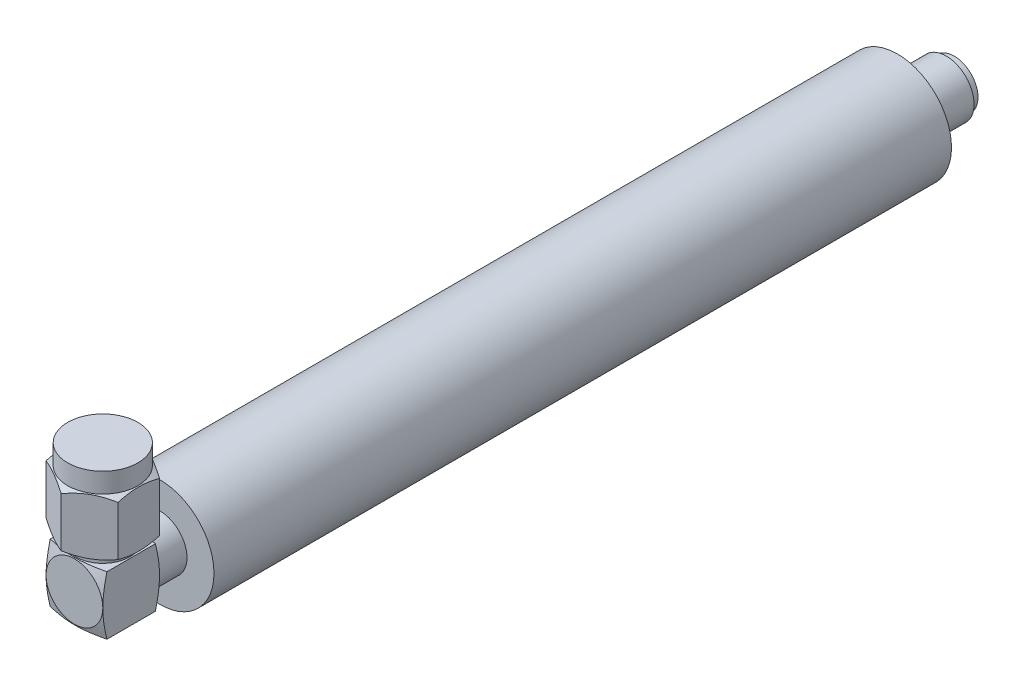
SolidWorks part; units mm, degrees
ref_plane "Front Plane" through (0, 0, 0) normal (0, 0, 1) x (1, 0, 0)
ref_plane "Top Plane" through (0, 0, 0) normal (0, 1, 0) x (1, 0, 0)
ref_plane "Right Plane" through (0, 0, 0) normal (1, 0, 0) x (0, 0, -1)
sketch "Sketch1" plane through (0, 0, 0) normal (0, 0, 1) x (1, 0, 0)
  circle A0 centre (0, 0) radius 6
  dimension "D1" = 12
extrude "Boss-Extrude1" add sketch "Sketch1" along normal blind 81.92
sketch "Sketch2" plane through (0, 0, 0) normal (0, 1, 0) x (1, 0, 0)
  line L0 (0, -88.8627) -> (0, -94.8627) construction
  line L1 (-1.9871, 0) -> (-1.9871, 1.5)
  line L2 (6, 0) -> (-6, 0) construction
  line L3 (-1.9871, 1.5) -> (-3.1, 1.5)
  line L4 (-3.1, 1.5) -> (-3.1, 6.3)
  line L5 (-3.1, 6.3) -> (0, 6.3)
  line L6 (-1.9871, 0) -> (0, 0)
  line L7 (0, 6.3) -> (0, 0)
  dimension "D1" = 6.3
  dimension "D2" = 1.5
  dimension "D3" = 6.2
revolve "Revolve1" add sketch "Sketch2" angle 360 about L0
sketch "Sketch3" plane through (0, 0, 81.92) normal (0, 0, 1) x (1, 0, 0)
  circle A0 centre (0, 0) radius 3
  dimension "D1" = 6
extrude "Boss-Extrude2" add sketch "Sketch3" along normal blind 3.2
sketch "Sketch4" plane through (0, 0, 0) normal (0, 1, 0) x (1, 0, 0)
  line L0 (-3, -85.12) -> (3, -85.12) construction
  line L1 (-3.15, -91.42) -> (3.15, -91.42)
  line L2 (-3.15, -91.42) -> (-3.15, -85.12)
  line L3 (-3.15, -85.12) -> (3.15, -85.12)
  line L4 (3.15, -91.42) -> (3.15, -85.12)
  line L5 (-3.15, -91.42) -> (3.15, -85.12) construction
  line L6 (-3.15, -85.12) -> (3.15, -91.42) construction
  line L7 (-3, -81.92) -> (3, -81.92) construction
  point P0 (0, -88.27)
  dimension "D1" = 6.3
  dimension "D2" = 6.3
  dimension "D3" = 6.35
extrude "Boss-Extrude3" add sketch "Sketch4" along normal mid plane 6.5
sketch "Sketch9" plane through (0, 0, 0) normal (0, 1, 0) x (1, 0, 0)
  line L0 (0, -97.0404) -> (0, -73.5237) construction
  line L1 (-3.15, -91.42) -> (-4.65, -90.92)
  line L4 (-4.65, -90.92) -> (-4.65, -91.42)
  line L5 (-4.65, -91.42) -> (-3.15, -91.42)
  line L6 (-3.15, -85.12) -> (-4.65, -85.12)
  line L8 (-4.65, -85.12) -> (-4.65, -85.62)
  line L9 (-3.15, -85.12) -> (-4.65, -85.62)
  dimension "D1" = 1.5
  dimension "D2" = 0.5
  dimension "D3" = 1.5
  dimension "D4" = 0.5
  dimension "D5" = 3.15
  dimension "D6" = 3.15
revolve "Cut-Revolve3" cut sketch "Sketch9" angle 360 about L0
sketch "Sketch10" plane through (0, 3.25, 0) normal (0, 1, 0) x (1, 0, 0)
  line L0 (-3, -81.92) -> (3, -81.92) construction
  circle A0 centre (0, -88.27) radius 3
  dimension "D1" = 6
  dimension "D2" = 6.35
extrude "Boss-Extrude6" add sketch "Sketch10" along normal mid plane 2
sketch "Sketch11" plane through (0, 4.25, 0) normal (0, 1, 0) x (1, 0, 0)
  line L1 (0, -83.6512) -> (-4, -85.9606)
  line L2 (-4, -85.9606) -> (-4, -90.5794)
  line L3 (-4, -90.5794) -> (0, -92.8888)
  line L4 (0, -92.8888) -> (4, -90.5794)
  line L5 (4, -90.5794) -> (4, -85.9606)
  line L6 (4, -85.9606) -> (0, -83.6512)
  circle A0 centre (0, -88.27) radius 4 construction
  point P1 (2, -84.8059)
  dimension "D1" = 8
extrude "Boss-Extrude7" add sketch "Sketch11" along normal blind 8.5
sketch "Sketch12" plane through (0, 12.75, 0) normal (0, 1, 0) x (1, 0, 0)
  line L0 (-3, -81.92) -> (3, -81.92) construction
  circle A0 centre (0, -88.27) radius 3.9
  circle A1 centre (0, -88.27) radius 5.6457
  dimension "D2" = 7.8
  dimension "D1" = 6.35
extrude "Cut-Extrude2" cut sketch "Sketch12" against normal blind 2.2
sketch "Sketch13" plane through (0, 0, 0) normal (1, 0, 0) x (0, 0, -1)
  line L0 (-92.17, 10.55) -> (-92.8888, 10.15)
  line L1 (-92.8888, 10.55) -> (-92.8888, 4.25) construction
  line L2 (-92.8888, 10.15) -> (-92.8888, 10.55)
  line L3 (-92.8888, 10.55) -> (-92.17, 10.55)
  line L4 (-88.27, 13.7522) -> (-88.27, 2.0185) construction
  line L5 (-92.8888, 4.65) -> (-92.17, 4.25)
  line L6 (-92.8888, 4.25) -> (-90.5794, 4.25) construction
  line L7 (-92.17, 4.25) -> (-92.8888, 4.25)
  line L8 (-92.8888, 4.25) -> (-92.8888, 4.65)
  dimension "D1" = 0.4
  dimension "D2" = 0.4
  dimension "D3" = 3.9
revolve "Cut-Revolve4" cut sketch "Sketch13" angle 360 about L4
sketch "Sketch14" plane through (0, 0, -6.3) normal (0, 0, -1) x (-1, 0, 0)
  circle A0 centre (0, 0) radius 2.65
  circle A1 centre (0, 0) radius 3.9598
  dimension "D1" = 5.3
extrude "Cut-Extrude3" cut sketch "Sketch14" against normal blind 0.89
sketch "Sketch15" plane through (0, 0, 0) normal (0, 1, 0) x (1, 0, 0)
  line L0 (0, 16.0171) -> (0, -97.2418) construction
